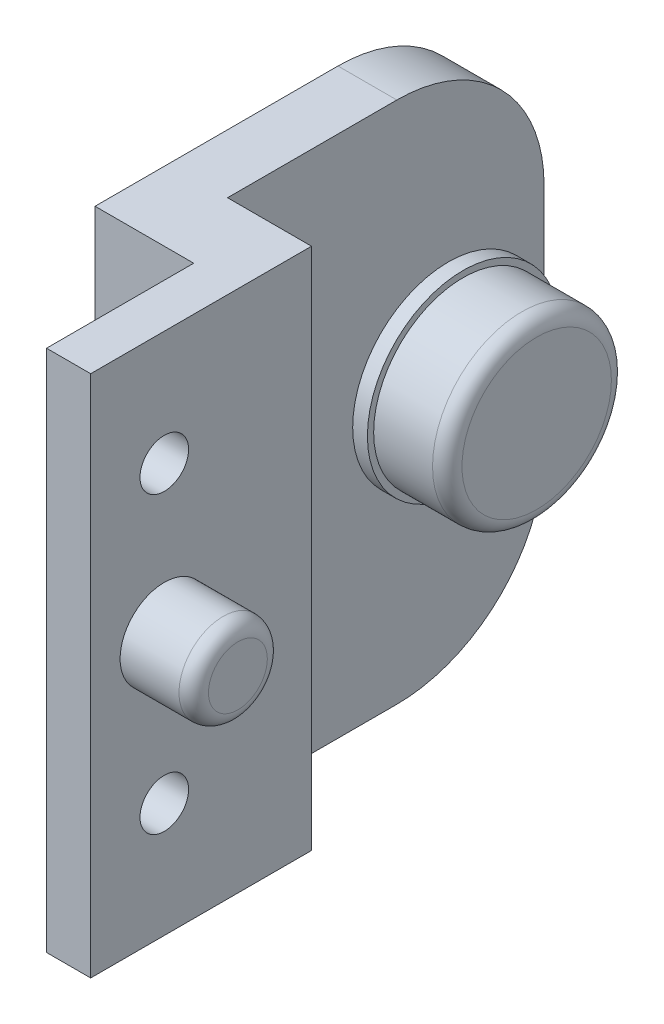
SolidWorks part; units mm, degrees
ref_plane "Front Plane" through (0, 0, 0) normal (0, 0, 1) x (1, 0, 0)
ref_plane "Top Plane" through (0, 0, 0) normal (0, 1, 0) x (1, 0, 0)
ref_plane "Right Plane" through (0, 0, 0) normal (1, 0, 0) x (0, 0, -1)
sketch "Sketch4" plane through (0, 0, 0) normal (0, 0, 1) x (1, 0, 0)
  line L1 (-6.23, -9.975) -> (6.23, -9.975)
  line L2 (-6.23, -9.975) -> (-6.23, 7.275)
  line L3 (-6.23, 7.275) -> (6.23, 7.275)
  line L4 (6.23, -9.975) -> (6.23, 7.275)
  point P4 (0, 7.275)
  dimension "D1" = 12.46
  dimension "D2" = 17.25
  dimension "D3" = 9.975
extrude "Boss-Extrude3" add sketch "Sketch4" along normal blind 6
sketch "Sketch8" plane through (0, -9.975, 0) normal (0, -1, 0) x (-1, 0, 0)
  circle A0 centre (0, -23.55) radius 12.5468
  circle A1 centre (0, -23.55) radius 11.15
  dimension "D1" = 22.3
  dimension "D2" = 23.55
extrude "Boss-Extrude6" add sketch "Sketch8" along normal blind 8.3 and the other way up to surface (17.25 mm away) other way up to face at (0, 7.275, 3)
sketch "Sketch5" plane through (0, 7.275, 0) normal (0, 1, 0) x (1, 0, 0)
  line L8 (12.5468, -23.55) -> (12.5468, 0)
  line L9 (12.5468, 0) -> (6.23, 0)
  line L10 (-12.5468, -23.55) -> (-12.5468, 0)
  line L11 (-12.5468, 0) -> (-6.23, 0)
  line L12 (-6.23, 0) -> (-6.23, -29.7)
  line L14 (6.23, -29.7) -> (6.23, 0)
  line L15 (-6.23, -29.7) -> (6.23, -29.7)
  line L16 (6.23, -6) -> (-6.23, -6) construction
  circle A0 centre (0, -23.55) radius 12.5468 construction
  arc A1 (-12.5468, -23.55) -> (12.5468, -23.55) centre (0, -23.55) ccw
  dimension "D1" = 23.7
  dimension "D2" = 23.55
extrude "Boss-Extrude4" add sketch "Sketch5" against normal up to surface (17.25 mm away) up to face at (0, -9.975, 3)
sketch "Sketch6" plane through (0, 7.275, 0) normal (0, 1, 0) x (1, 0, 0)
  line L0 (6.23, -6) -> (-6.23, -6) construction
  line L3 (6.23, -29.7) -> (-6.23, -29.7) construction
  circle A0 centre (0, -3.6) radius 0.75
  circle A1 centre (0, -32.1) radius 0.75
  dimension "D1" = 1.5
  dimension "D3" = 1.5
  dimension "D2" = 2.4
  dimension "D4" = 2.4
extrude "Cut-Extrude1" cut sketch "Sketch6" against normal blind 5
chamfer "Chamfer1" distance 0.5 angle 60 2 edges at (0, 7.275, 4.35) (0, 7.275, 32.85)
sketch "Sketch10" plane through (0, 7.275, 0) normal (0, 1, 0) x (1, 0, 0)
  line L1 (-6.23, -6) -> (6.23, -6)
  line L2 (-6.23, -6) -> (-6.23, -29.7)
  line L3 (-6.23, -29.7) -> (6.23, -29.7)
  line L4 (6.23, -6) -> (6.23, -29.7)
extrude "Cut-Extrude3" cut sketch "Sketch10" against normal up to surface (17.25 mm away) up to face at (0, -9.975, 10.3399)
ref_plane "Plane1" through (0, 0, 36.0968) normal (0, 0, 1) x (1, 0, 0)
sketch "Sketch13" plane through (0, -18.275, 0) normal (0, -1, 0) x (1, 0, 0)
  line L0 (-12.5468, 23.55) -> (-12.5468, 0)
  line L1 (-12.5468, 0) -> (12.5468, 0)
  line L2 (12.5468, 0) -> (12.5468, 23.55)
  arc A0 (-12.5468, 23.55) -> (12.5468, 23.55) centre (0, 23.55) ccw
  point P3 (0, 0)
extrude "Boss-Extrude7" add sketch "Sketch13" against normal up to surface (8.3 mm away) up to face at (0, -9.975, 10.3399)
sketch "Sketch15" plane through (0, 7.275, 0) normal (0, 1, 0) x (1, 0, 0)
  line L0 (-12.5468, 0) -> (12.5468, 0)
  line L1 (12.5468, 0) -> (12.5468, -23.55)
  line L2 (-12.5468, 0) -> (-12.5468, -23.55)
  line L3 (6.23, -6) -> (6.23, -29.7) construction
  line L4 (-6.23, -0.8) -> (6.23, -0.8)
  line L5 (-6.23, -0.8) -> (-6.23, -33)
  line L6 (-4.73, -34.5) -> (4.73, -34.5)
  line L7 (6.23, -0.8) -> (6.23, -33)
  arc A0 (-12.5468, -23.55) -> (12.5468, -23.55) centre (0, -23.55) ccw
  circle A1 centre (0, -3.6) radius 0.75 construction
  arc A2 (4.73, -34.5) -> (6.23, -33) centre (4.73, -33) ccw
  arc A3 (-6.23, -33) -> (-4.73, -34.5) centre (-4.73, -33) ccw
  point P15 (0, -0.8)
  dimension "D1" = 0.8
  dimension "D3" = 1.5
  dimension "D2" = 2.8
  dimension "D4" = 0
  dimension "D5" = 34.5
extrude "Boss-Extrude9" add sketch "Sketch15" along normal blind 10
sketch "Sketch20" plane through (0, -18.275, 0) normal (0, -1, 0) x (1, 0, 0)
  circle A0 centre (0, 23.55) radius 7.15
  circle A1 centre (0, 23.55) radius 11.15
  circle A2 centre (0, 23.55) radius 11.15 construction
  dimension "D1" = 14.3
extrude "Boss-Extrude11" add sketch "Sketch20" against normal up to surface (8.3 mm away) up to face at (0, -9.975, 27.1007)
sketch "Sketch21" plane through (0, -18.275, 0) normal (0, -1, 0) x (1, 0, 0)
  circle A0 centre (0, 23.55) radius 7.15
  circle A1 centre (0, 23.55) radius 10.15
  circle A2 centre (0, 23.55) radius 7.15 construction
  dimension "D1" = 20.3
extrude "Cut-Extrude7" cut sketch "Sketch21" against normal blind 1.3
sketch "Sketch11" plane through (0, 0, 29.7) normal (0, 0, 1) x (1, 0, 0)
  line L1 (-5, -9.975) -> (5, -9.975)
  line L2 (-5, -9.975) -> (-5, -11.975)
  line L3 (-5, -11.975) -> (5, -11.975)
  line L4 (5, -9.975) -> (5, -11.975)
  line L5 (-3.6469, -9.975) -> (3.6469, -9.975) construction
  point P4 (0, -9.975)
  dimension "D1" = 0
  dimension "D2" = 10
  dimension "D3" = 2
extrude "Cut-Extrude4" cut sketch "Sketch11" against normal up to surface (23.7 mm away) up to face at (0, -1.35, 6)
sketch "Sketch25" plane through (0, -18.275, 0) normal (0, -1, 0) x (1, 0, 0)
  line L0 (6.23, 20.0415) -> (6.23, 6) construction
  line L1 (-6.23, 6) -> (6.23, 6)
  line L2 (-6.23, 6) -> (-6.23, 12)
  line L3 (-6.23, 12) -> (6.23, 12)
  line L4 (6.23, 6) -> (6.23, 12)
  dimension "D1" = 6
extrude "Cut-Extrude8" cut sketch "Sketch25" against normal up to next
sketch "Sketch17" plane through (0, 17.275, 0) normal (0, 1, 0) x (1, 0, 0)
  line L0 (22.25, 26.5) -> (22.25, 0)
  line L1 (22.25, 0) -> (-22.25, 0)
  line L2 (-22.25, 0) -> (-22.25, 26.5)
  line L3 (-22.25, 26.5) -> (-18.25, 26.5)
  line L4 (-18.25, 26.5) -> (-18.25, 5)
  line L5 (-18.25, 5) -> (18.25, 5)
  line L6 (18.25, 5) -> (18.25, 26.5)
  line L7 (18.25, 26.5) -> (22.25, 26.5)
  point P2 (0, 5)
  point P10 (0, 0)
  dimension "D1" = 4
  dimension "D2" = 36.5
  dimension "D3" = 0
  dimension "D4" = 26.5
  dimension "D5" = 5
extrude "Boss-Extrude10" add sketch "Sketch17" against normal up to surface (35.55 mm away)
sketch "Sketch18" plane through (18.25, 0, 0) normal (-1, 0, 0) x (0, 0, 1)
  line L0 (-26.5, -18.275) -> (-26.5, 17.275) construction
  line L1 (-26.5, 5.2191) -> (-5, 5.2191)
  line L2 (-26.5, 5.2191) -> (-26.5, -6.2191)
  line L3 (-26.5, -6.2191) -> (-5, -6.2191)
  line L4 (-5, 5.2191) -> (-5, -6.2191)
  line L5 (-5, -18.275) -> (-5, 17.275) construction
  point P6 (-26.5, -0.5)
  point P7 (-26.5, -0.5)
  dimension "D1" = 0
extrude "Cut-Extrude5" cut sketch "Sketch18" against normal blind 2
sketch "Sketch19" plane through (20.25, 0, 0) normal (-1, 0, 0) x (0, 0, 1)
  line L0 (-26.5, -18.275) -> (-26.5, 17.275) construction
  circle A0 centre (-20, -0.5) radius 3.5
  point P4 (-26.5, -0.5)
  dimension "D1" = 7
  dimension "D2" = 6.5
  dimension "D3" = 0
extrude "Cut-Extrude6" cut sketch "Sketch19" against normal through all both and the other way through all
fillet "Fillet1" radius 10 4 edges at (20.25, -18.275, -26.5) (20.25, 17.275, -26.5) (-20.25, 17.275, -26.5) (-20.25, -18.275, -26.5)
ref_plane "Plane2" through (0, 0, 0) normal (1, 0, 0) x (0, 0, -1)
ref_plane "Plane3" through (0, -0.5, 0) normal (0, -1, 0) x (-1, 0, 0)
sketch "Sketch22" plane through (-22.25, 0, 0) normal (-1, 0, 0) x (0, 0, 1)
  circle A0 centre (-20, -0.5) radius 6.5
  dimension "D1" = 13
extrude "Boss-Extrude12" add sketch "Sketch22" against normal blind 5
sketch "Sketch23" plane through (-17.25, 0, 0) normal (1, 0, 0) x (0, 0, -1)
  circle A0 centre (20, -0.5) radius 6.075
  dimension "D1" = 12.15
extrude "Boss-Extrude13" add sketch "Sketch23" along normal blind 5
fillet "Fillet2" radius 1 1 edges at (-12.25, -0.5, -26.075)
sketch "Sketch26" plane through (20.25, 0, 0) normal (-1, 0, 0) x (0, 0, 1)
  line L0 (-5, 2) -> (-20, 2.6585)
  line L1 (-5, -18.275) -> (-5, 17.275) construction
  line L4 (-5, 5.2191) -> (-5, 2)
  line L6 (-26.5, 5.2191) -> (-5, 5.2191)
  line L7 (-20, -3.6585) -> (-5, -3)
  line L8 (-5, -3) -> (-5, -6.2191)
  line L9 (-24.475, -0.5) -> (24.475, -0.5) construction
  line L11 (-26.5, -6.2191) -> (-5, -6.2191)
  line L12 (-20, 2.6585) -> (-26.5, 2.9439)
  line L13 (-20, -3.6585) -> (-26.5, -3.9438)
  line L14 (-26.5, -3.9438) -> (-26.5, -6.2191)
  line L16 (-26.5, 2.9439) -> (-26.5, 5.2191)
  line L18 (-26.5, -8.275) -> (-26.5, 7.275) construction
  circle A0 centre (-20, -0.5) radius 3.5 construction
  dimension "D1" = 5
  dimension "D2" = 2.5
  dimension "D3" = 0
  dimension "D4" = 6.317
  dimension "D5" = 3.1585
  dimension "D6" = 180
  dimension "D7" = 180
extrude "Boss-Extrude14" add sketch "Sketch26" along normal up to surface (2 mm away) up to face at (18.25, 10.8669, -16.3142)
sketch "Sketch27" plane through (22.25, 0, 0) normal (1, 0, 0) x (0, 0, -1)
  line L0 (-24.475, -0.5) -> (24.475, -0.5) construction
  circle A0 centre (10, -0.5) radius 0.75
  circle A1 centre (20, -0.5) radius 3.5 construction
  dimension "D2" = 1.5
  dimension "D1" = 10
extrude "Cut-Extrude9" cut sketch "Sketch27" against normal up to next
sketch "Sketch28" plane through (0, 17.275, 0) normal (0, 1, 0) x (1, 0, 0)
  line L0 (-12.5468, 11.805) -> (-12.5468, -42.7563)
  line L1 (-12.5468, -42.7563) -> (39.6891, -42.7563)
  line L2 (39.6891, -42.7563) -> (38.7036, 30.9776)
  line L3 (38.7036, 30.9776) -> (-8.6008, 28.3795)
  line L4 (-8.6008, 28.3795) -> (-12.5468, 11.805)
extrude "Cut-Extrude10" cut sketch "Sketch28" against normal through all
sketch "Sketch29" plane through (0, 0, 0) normal (0, 0, 1) x (1, 0, 0)
  line L0 (-22.25, -18.275) -> (-12.5468, -18.275) construction
  line L1 (-12.5468, 17.275) -> (-15.5468, 17.275)
  line L2 (-12.5468, 17.275) -> (-12.5468, -18.275)
  line L3 (-12.5468, -18.275) -> (-15.5468, -18.275)
  line L4 (-15.5468, 17.275) -> (-15.5468, -18.275)
  dimension "D1" = 3
extrude "Boss-Extrude15" add sketch "Sketch29" along normal blind 10
sketch "Sketch30" plane through (-12.5468, 0, 0) normal (1, 0, 0) x (0, 0, -1)
  line L0 (-10, -18.275) -> (-10, 17.275) construction
  circle A0 centre (-5, -0.5) radius 3
  dimension "D1" = 6
  dimension "D2" = 5
extrude "Boss-Extrude16" add sketch "Sketch30" along normal blind 5
fillet "Fillet3" radius 1 1 edges at (-7.5468, -0.5, 2)
sketch "Sketch31" plane through (0, 0, 0) normal (1, 0, 0) x (0, 0, -1)
  line L0 (-10, -18.275) -> (-10, 17.275) construction
  circle A0 centre (-5, 9.5) radius 1.65
  circle A1 centre (-5, -10.5) radius 1.65
  circle A3 centre (-5, -0.5) radius 2 construction
  dimension "D3" = 5
  dimension "D4" = 3.3
  dimension "D5" = 3.3
  dimension "D1" = 10
  dimension "D2" = 10
extrude "Cut-Extrude11" cut sketch "Sketch31" against normal through all
